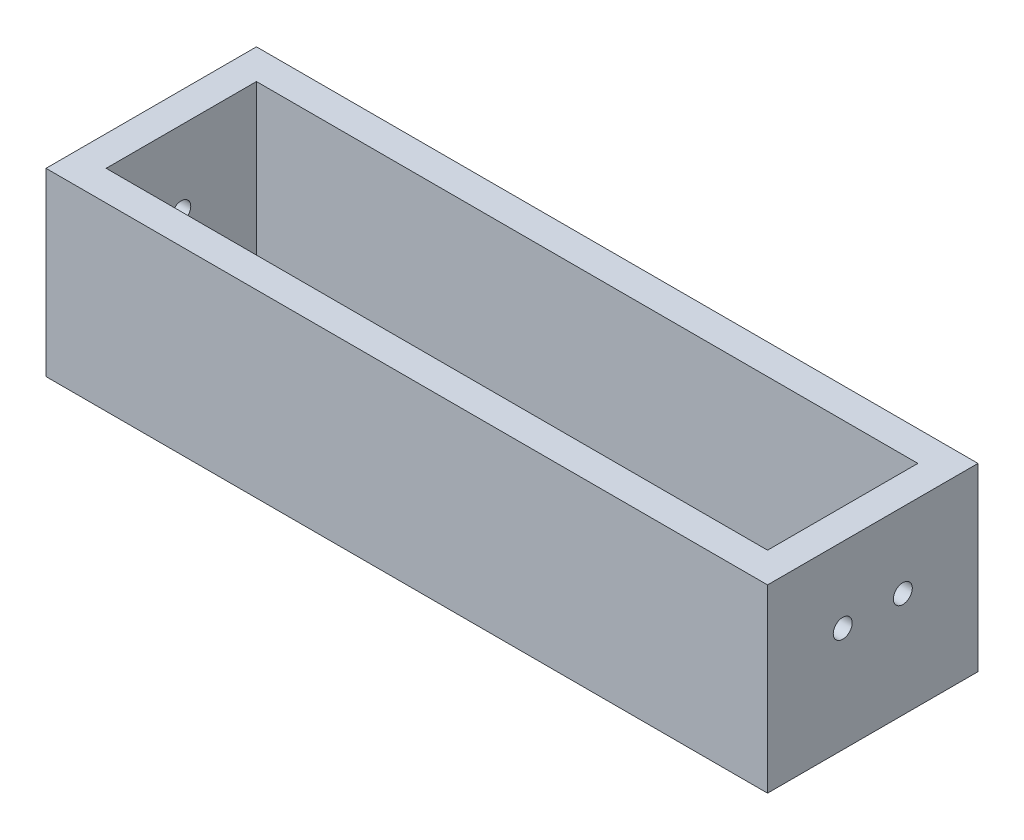
SolidWorks part; units mm, degrees
ref_plane "Front Plane" through (0, 0, 0) normal (0, 0, 1) x (1, 0, 0)
ref_plane "Top Plane" through (0, 0, 0) normal (0, 1, 0) x (1, 0, 0)
ref_plane "Right Plane" through (0, 0, 0) normal (1, 0, 0) x (0, 0, -1)
sketch "Sketch1" plane through (0, 0, 0) normal (0, 1, 0) x (1, 0, 0)
  line L1 (-38.1, -11.1125) -> (38.1, -11.1125)
  line L2 (-38.1, -11.1125) -> (-38.1, 11.1125)
  line L3 (-38.1, 11.1125) -> (38.1, 11.1125)
  line L4 (38.1, -11.1125) -> (38.1, 11.1125)
  line L5 (-38.1, -11.1125) -> (38.1, 11.1125) construction
  line L6 (-38.1, 11.1125) -> (38.1, -11.1125) construction
  point P0 (0, 0)
  dimension "D1" = 76.2
  dimension "D2" = 22.225
extrude "Boss-Extrude1" add sketch "Sketch1" along normal blind 3.175
sketch "Sketch2" plane through (0, 3.175, 0) normal (0, 1, 0) x (1, 0, 0)
  line L0 (-38.1, 11.1125) -> (-38.1, -11.1125) construction
  line L1 (-38.1, 11.1125) -> (38.1, 11.1125)
  line L2 (-38.1, 11.1125) -> (-38.1, 7.9375)
  line L3 (-38.1, 7.9375) -> (38.1, 7.9375)
  line L4 (38.1, 11.1125) -> (38.1, 7.9375)
  line L5 (38.1, -11.1125) -> (-38.1, -11.1125)
  line L6 (38.1, -11.1125) -> (38.1, -7.9375)
  line L7 (38.1, -7.9375) -> (-38.1, -7.9375)
  line L8 (-38.1, -11.1125) -> (-38.1, -7.9375)
  line L9 (38.1, -11.1125) -> (38.1, 11.1125) construction
  line L11 (38.1, 7.9375) -> (34.925, 7.9375)
  line L12 (38.1, 7.9375) -> (38.1, -7.9375)
  line L13 (38.1, -7.9375) -> (34.925, -7.9375)
  line L14 (34.925, 7.9375) -> (34.925, -7.9375)
  line L15 (-38.1, 7.9375) -> (-34.925, 7.9375)
  line L16 (-38.1, 7.9375) -> (-38.1, -7.9375)
  line L17 (-38.1, -7.9375) -> (-34.925, -7.9375)
  line L18 (-34.925, 7.9375) -> (-34.925, -7.9375)
  line M9 (38.1, -11.1125) -> (38.1, 11.1125)
  line M10 (38.1, 11.1125) -> (-38.1, 11.1125)
  line M11 (-38.1, 11.1125) -> (-38.1, -11.1125)
  line M12 (-38.1, -11.1125) -> (38.1, -11.1125)
  dimension "D1" = 3.175
extrude "Boss-Extrude2" add sketch "Sketch2" along normal blind 15.875 contours L3 M11 M9 M10 | L18 L3 L7 M11 | L7 M9 M11 M12 | L3 L14 L7 M9
sketch "Sketch3" plane through (34.925, 0, 0) normal (-1, 0, 0) x (0, 0, 1)
  line L0 (0, 19.05) -> (0, 3.175) construction
  line L1 (-7.9375, 19.05) -> (7.9375, 19.05) construction
  line L2 (-7.9375, 3.175) -> (7.9375, 3.175) construction
  circle A0 centre (3.175, 11.1125) radius 1
  circle A1 centre (-3.175, 11.1125) radius 1
  point P4 (0, 0)
  dimension "D2" = 2
  dimension "D1" = 6.35
  dimension "D3" = 7.9375
  dimension "D4" = 7.9375
extrude "Cut-Extrude1" cut sketch "Sketch3" against normal through all contours A1 | A0
sketch "Sketch4" plane through (-34.925, 0, 0) normal (1, 0, 0) x (0, 0, -1)
  line L0 (-7.9375, 19.05) -> (-7.9375, 3.175) construction
  line L1 (7.9375, 3.175) -> (-7.9375, 3.175) construction
  circle A0 centre (0, 11.1125) radius 1
  point P2 (0, 0)
  point P5 (-7.9375, 11.1125)
  point P8 (0, 3.175)
  dimension "D1" = 2
extrude "Cut-Extrude2" cut sketch "Sketch4" against normal through all
